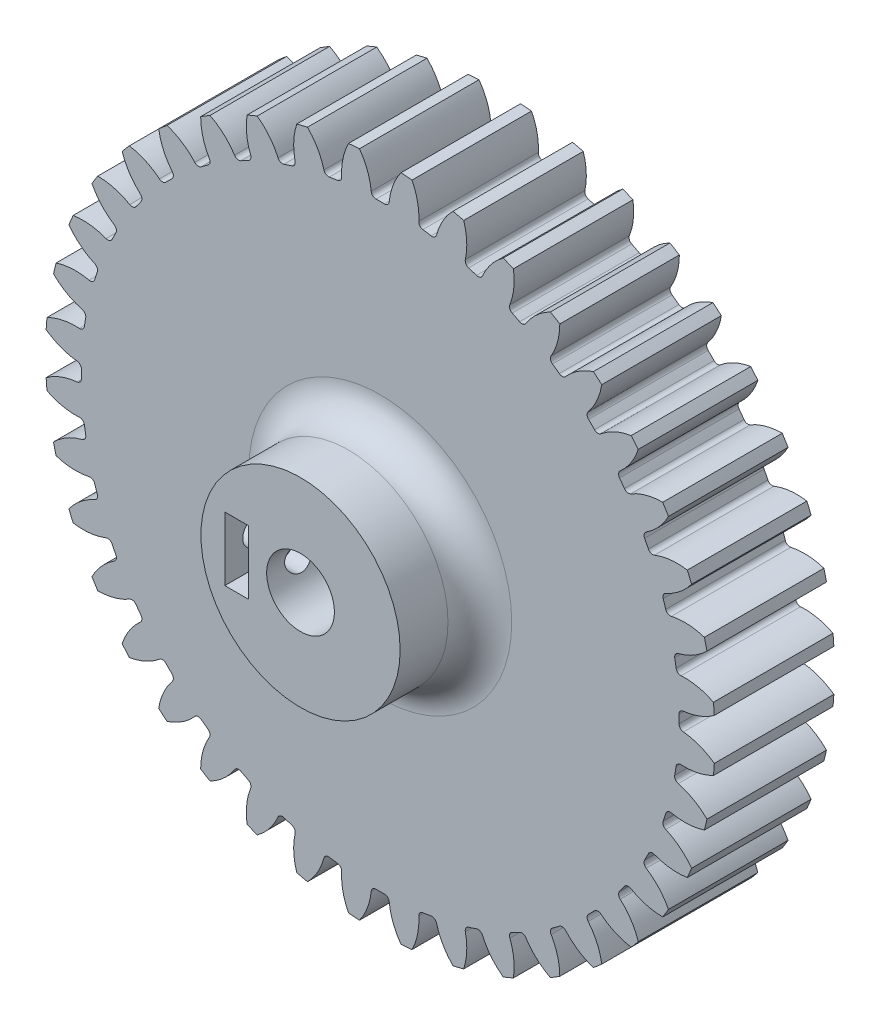
SolidWorks part; units mm, degrees
ref_plane "Alzado" through (0, 0, 0) normal (0, 0, 1) x (1, 0, 0)
ref_plane "Planta" through (0, 0, 0) normal (0, 1, 0) x (1, 0, 0)
ref_plane "Vista lateral" through (0, 0, 0) normal (1, 0, 0) x (0, 0, -1)
sketch "Croquis1" plane through (0, 0, 0) normal (0, 0, 1) x (1, 0, 0)
  circle A0 centre (0, 0) radius 40
  circle A1 centre (0, 0) radius 42
  circle A2 centre (0, 0) radius 37.5
  dimension "D1" = 80
  dimension "D2" = 84
  dimension "D3" = 4.5
extrude "Saliente-Extruir1" add sketch "Croquis1" along normal mid plane 15 contours A1
sketch "Croquis2" plane through (0, 0, 0) normal (0, 0, 1) x (1, 0, 0)
  line L0 (0, 0) -> (0, 42) construction
  line L1 (-1.5704, 39.9692) -> (1.5704, 39.9692) construction
  line L2 (-1.0947, 37.484) -> (0, 0) construction
  line L3 (-2.6439, 42.9186) -> (0, 35.6545) construction
  line L4 (0, 0) -> (3.2953, 41.8705) construction
  line L5 (1.5704, 39.9692) -> (4.7015, 39.7227) construction
  circle A0 centre (0, 0) radius 42 construction
  arc A3 (-1.0947, 37.484) -> (-3.413, 42.8643) centre (-9.0354, 37.2521) ccw
  arc A4 (1.0947, 37.484) -> (3.413, 42.8643) centre (9.0354, 37.2521) cw
  circle A5 centre (0, 0) radius 37.5 construction
  arc A7 (1.0947, 37.484) -> (-1.0947, 37.484) centre (0, 0) ccw
  circle A9 centre (0, 0) radius 40 construction
  circle A10 centre (0, 0) radius 43
  arc A11 (3.413, 42.8643) -> (-3.413, 42.8643) centre (0, 0) ccw
  dimension "D2" = 20
  dimension "D3" = 4.5
  dimension "D1" = 1
extrude "Cortar-Extruir1" cut sketch "Croquis2" against normal through all and the other way through all
fillet "Redondeo1" radius 0.6 2 edges at (1.0947, 37.484, 0) (-1.0947, 37.484, 0)
pattern_circular "MatrizC1" count 40 over 360 about axis through (0, 0, 0) along (0, 0, 1) of "Redondeo1", "Cortar-Extruir1"
sketch "Croquis3" plane through (0, 0, 0) normal (0, 0, 1) x (1, 0, 0)
  circle A0 centre (0, 0) radius 4.25
  dimension "D1" = 8.5
extrude "Cortar-Extruir2" cut sketch "Croquis3" against normal up to surface (15 mm away) from surface at 7.5 up to face at (0, 0, -7.5) starting at face at (0, 0, 7.5)
sketch "Croquis4" plane through (0, 0, 0) normal (0, 0, 1) x (1, 0, 0)
  circle A0 centre (0, 0) radius 4.25
  circle A1 centre (0, 0) radius 12.5
  dimension "D1" = 25
extrude "Saliente-Extruir2" add sketch "Croquis4" along normal blind 10 from surface at 7.5 starting at face at (4.25, 0, 7.5)
sketch "Croquis5" plane through (0, 0, 0) normal (0, 0, 1) x (1, 0, 0)
  line L1 (-9.5, 4) -> (-6.5, 4)
  line L2 (-9.5, 4) -> (-9.5, -4)
  line L3 (-9.5, -4) -> (-6.5, -4)
  line L4 (-6.5, 4) -> (-6.5, -4)
  line L5 (-9.5, 4) -> (-6.5, -4) construction
  line L6 (-9.5, -4) -> (-6.5, 4) construction
  point P0 (-8, 0)
  dimension "D1" = 3
  dimension "D2" = 8
  dimension "D3" = 8
  dimension "D4" = 0
extrude "Cortar-Extruir3" cut sketch "Croquis5" against normal blind 8 from surface at 17.5 starting at face at (12.5, 0, 17.5)
sketch "Croquis6" plane through (0, 0, 0) normal (1, 0, 0) x (0, 0, -1)
  line L0 (-17.5, 12.5) -> (-17.5, -12.5) construction
  circle A0 centre (-13.5, 0) radius 1.75
  dimension "D1" = 3.5
  dimension "D2" = 4
extrude "Cortar-Extruir4" cut sketch "Croquis6" against normal up to surface (12.5 mm away)
fillet "Redondeo2" radius 4 1 edges at (12.5, 0, 7.5)
equation "\"Modulo\"= 2mm"
equation "\"Numero de Dientes\"= 40"
equation "\"D1@Croquis1\"=\"Modulo\"*\"Numero de Dientes\""
equation "\"D2@Croquis1\"=(\"Numero de Dientes\"+2)*\"Modulo\""
equation "\"D3@Croquis1\"=\"Modulo\"*if( \"Modulo\" =>1.25,2.25,2.4)"
equation "\"D3@Croquis2\"=180/\"Numero de Dientes\""
equation "\"D1@Redondeo1\"=.3*\"Modulo\""
equation "\"D1@MatrizC1\"=\"Numero de Dientes\""
